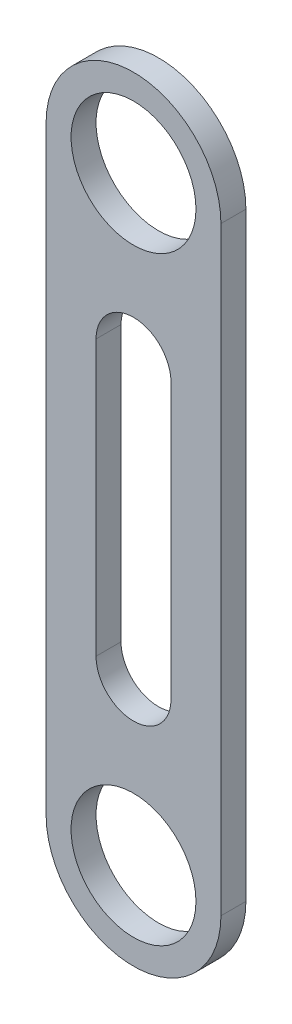
SolidWorks part; units mm, degrees
ref_plane "Front Plane" through (0, 0, 0) normal (0, 0, 1) x (1, 0, 0)
ref_plane "Top Plane" through (0, 0, 0) normal (0, 1, 0) x (1, 0, 0)
ref_plane "Right Plane" through (0, 0, 0) normal (1, 0, 0) x (0, 0, -1)
sketch "Sketch1" plane through (0, 0, 0) normal (0, 0, 1) x (1, 0, 0)
  line L0 (-7.9375, 76.2) -> (-11.1125, 76.2) construction
  line L1 (0, 68.2625) -> (0, 55.5625) construction
  line L2 (-11.1125, 76.2) -> (11.1125, 76.2)
  line L3 (-11.1125, 76.2) -> (-11.1125, 0)
  line L4 (-11.1125, 0) -> (11.1125, 0)
  line L5 (11.1125, 76.2) -> (11.1125, 0)
  line L6 (0, 7.9375) -> (0, 20.6375) construction
  line L7 (0, 20.6375) -> (0, 55.5625) construction
  line L8 (-4.7625, 20.6375) -> (-4.7625, 55.5625)
  line L9 (4.7625, 20.6375) -> (4.7625, 55.5625)
  circle A0 centre (0, 0) radius 7.9375 construction
  circle A1 centre (0, 76.2) radius 7.9375 construction
  circle A2 centre (0, 76.2) radius 7.9375
  circle A3 centre (0, 0) radius 7.9375
  arc A4 (-4.7625, 20.6375) -> (4.7625, 20.6375) centre (0, 20.6375) ccw
  arc A5 (4.7625, 55.5625) -> (-4.7625, 55.5625) centre (0, 55.5625) ccw
  circle A6 centre (0, 76.2) radius 11.1125
  circle A7 centre (0, 0) radius 11.1125
  point P16 (0, 38.1)
  dimension "D1" = 15.875
  dimension "D6" = 4.7625
  dimension "D2" = 76.2
  dimension "D3" = 3.175
  dimension "D4" = 22.225
  dimension "D5" = 12.7
extrude "Boss-Extrude1" add sketch "Sketch1" along normal blind 3.175 contours A3 L4 L5 L2 A2 L3 A5 L9 A4 L8 | A7 | A6
